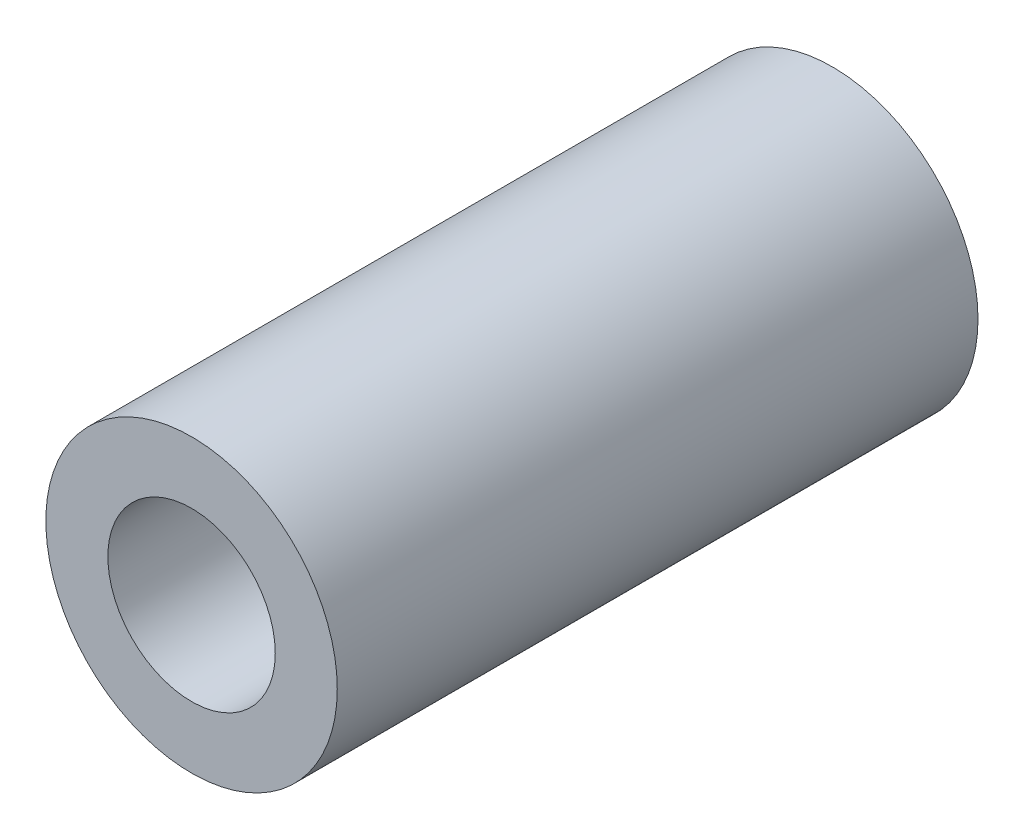
SolidWorks part; units mm, degrees
ref_plane "Front Plane" through (0, 0, 0) normal (0, 0, 1) x (1, 0, 0)
ref_plane "Top Plane" through (0, 0, 0) normal (0, 1, 0) x (1, 0, 0)
ref_plane "Right Plane" through (0, 0, 0) normal (1, 0, 0) x (0, 0, -1)
sketch "Sketch1" plane through (0, 0, 0) normal (0, 0, 1) x (1, 0, 0)
  circle A0 centre (0, 0) radius 4.05
  circle A2 centre (0, 0) radius 7.05
  dimension "D1" = 8.1
  dimension "D2" = 3
extrude "Boss-Extrude1" add sketch "Sketch1" along normal blind 31
imported_body "CARBONFIBERARROW.STEP<1>"
ref_plane "Front Plane-CARBONFIBERARROW" through (0, 0, 0) normal (0, 0, 1) x (1, 0, 0)
ref_plane "Top Plane-CARBONFIBERARROW" through (0, 0, 0) normal (0, 1, 0) x (1, 0, 0)
ref_plane "Right Plane-CARBONFIBERARROW" through (0, 0, 0) normal (1, 0, 0) x (0, 0, -1)
inserted part "CARBONFIBERARROW" parameters "D1.Boss-Extrude1"=150.47, "D1.Sketch2"=6.25, "D2.Sketch2"=7.65
